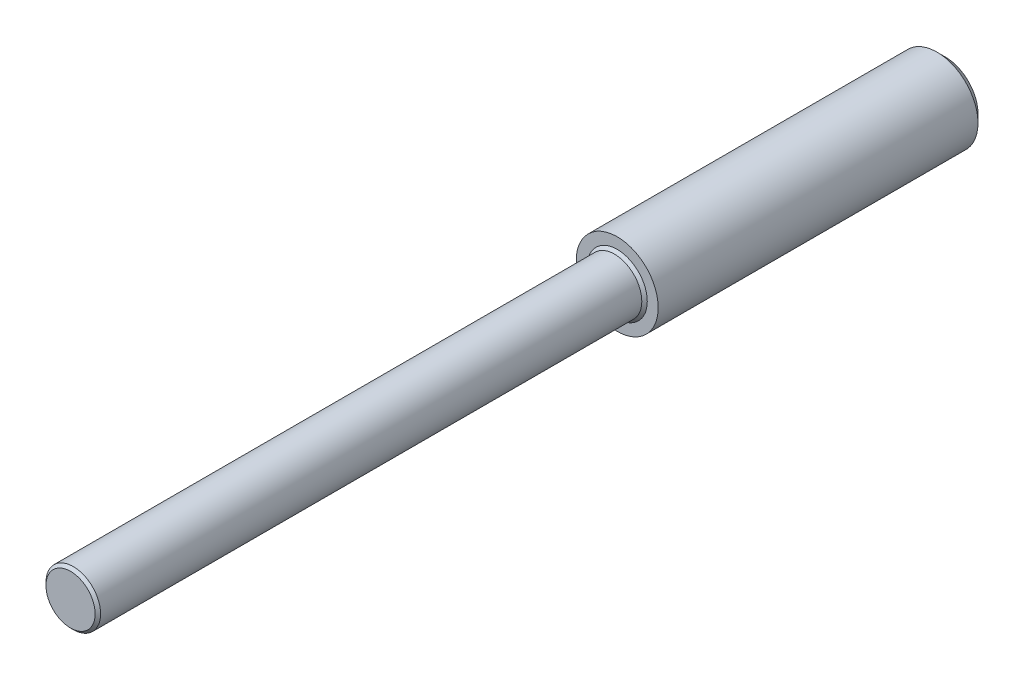
SolidWorks part; units mm, degrees
ref_plane "Front Plane" through (0, 0, 0) normal (0, 0, 1) x (1, 0, 0)
ref_plane "Top Plane" through (0, 0, 0) normal (0, 1, 0) x (1, 0, 0)
ref_plane "Right Plane" through (0, 0, 0) normal (1, 0, 0) x (0, 0, -1)
sketch "Sketch1" plane through (0, 0, 0) normal (0, 0, 1) x (1, 0, 0)
  circle A0 centre (0, 0) radius 1.5
  dimension "D1" = 3
extrude "Boss-Extrude1" add sketch "Sketch1" along normal blind 12
sketch "Sketch2" plane through (0, 0, 12) normal (0, 0, 1) x (1, 0, 0)
  circle A0 centre (0, 0) radius 1
  dimension "D1" = 2
extrude "Boss-Extrude2" add sketch "Sketch2" along normal blind 20
chamfer "Chamfer1" distance 0.3 angle 45 1 edges at (1.5, 0, 0)
chamfer "Chamfer2" distance 0.1 angle 45 2 edges at (1, 0, 12) (1, 0, 32)
